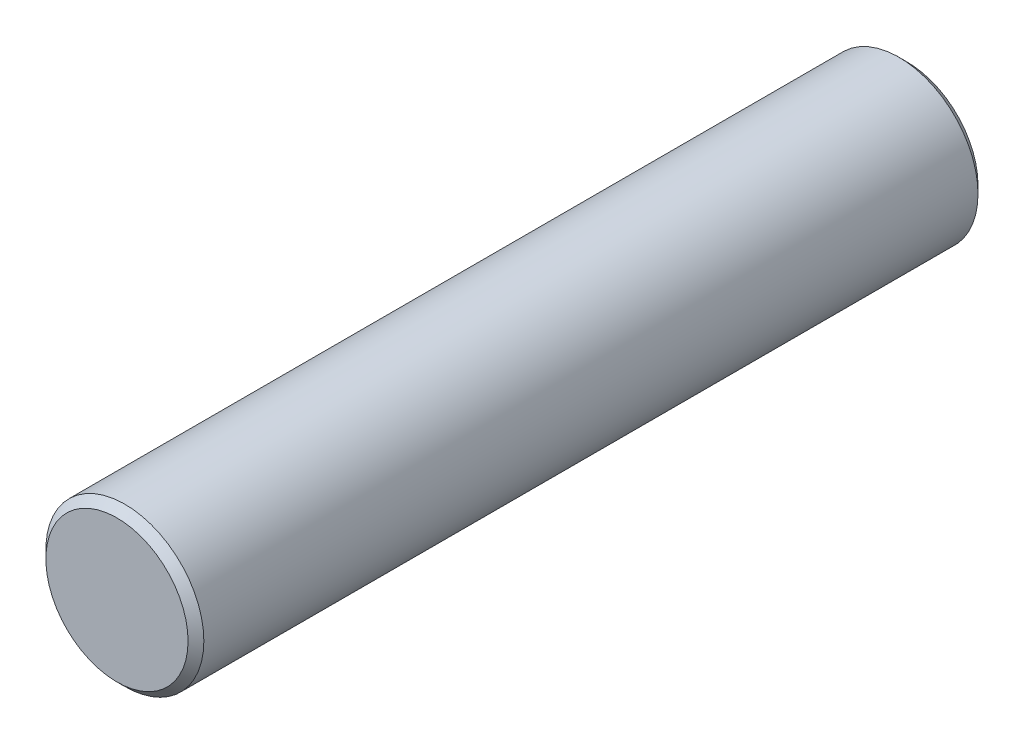
SolidWorks part; units mm, degrees
ref_plane "Plane1" through (0, 0, 0) normal (0, 0, 1) x (1, 0, 0)
ref_plane "Plane2" through (0, 0, 0) normal (0, 1, 0) x (1, 0, 0)
ref_plane "Plane3" through (0, 0, 0) normal (1, 0, 0) x (0, 0, -1)
sketch "Esquisse1" plane through (0, 0, 0) normal (0, 0, 1) x (1, 0, 0)
  circle A0 centre (0, 0) radius 2.5
  dimension "D1" = 5
extrude "Base-Extrusion" add sketch "Esquisse1" along normal blind 25
chamfer "Chanfrein1" distance 0.25 angle 45
